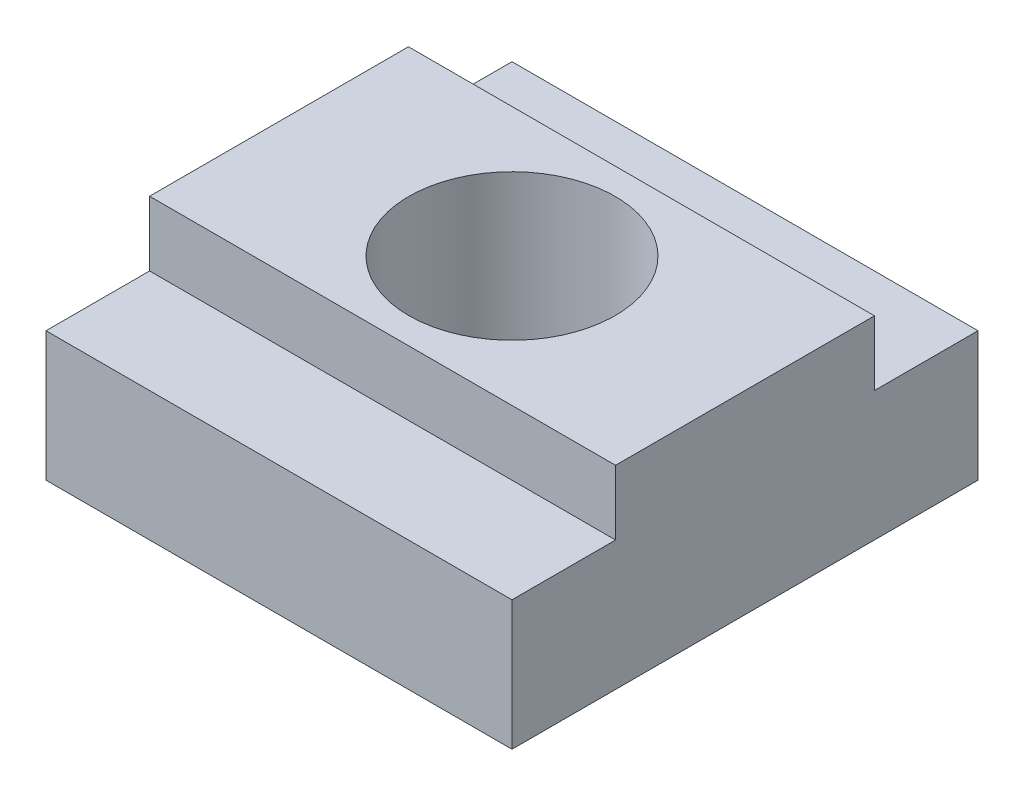
SolidWorks part; units mm, degrees
ref_plane "Front Plane" through (0, 0, 0) normal (0, 0, 1) x (1, 0, 0)
ref_plane "Top Plane" through (0, 0, 0) normal (0, 1, 0) x (1, 0, 0)
ref_plane "Right Plane" through (0, 0, 0) normal (1, 0, 0) x (0, 0, -1)
sketch "Sketch1" plane through (0, 0, 0) normal (1, 0, 0) x (0, 0, -1)
  line L0 (0, 0) -> (0, 11.9062) construction
  line L5 (7.9375, 11.9062) -> (-7.9375, 11.9062)
  line L6 (-7.9375, 11.9062) -> (-7.9375, 7.9375)
  line L7 (-7.9375, 7.9375) -> (-14.2875, 7.9375)
  line L8 (-14.2875, 7.9375) -> (-14.2875, 0)
  line L9 (-14.2875, 0) -> (14.2875, 0)
  line L10 (14.2875, 7.9375) -> (14.2875, 0)
  line L11 (7.9375, 7.9375) -> (14.2875, 7.9375)
  line L12 (7.9375, 11.9062) -> (7.9375, 7.9375)
  dimension "D1" = 14.2875
  dimension "D2" = 11.9062
  dimension "D3" = 7.9375
  dimension "D4" = 7.9375
extrude "Boss-Extrude1" add sketch "Sketch1" against normal mid plane 28.575
sketch "Sketch2" plane through (0, 11.9062, 0) normal (0, 1, 0) x (1, 0, 0)
  circle A0 centre (0, 0) radius 6.331
  dimension "D1" = 12.6619
extrude "Cut-Extrude1" cut sketch "Sketch2" against normal through all
